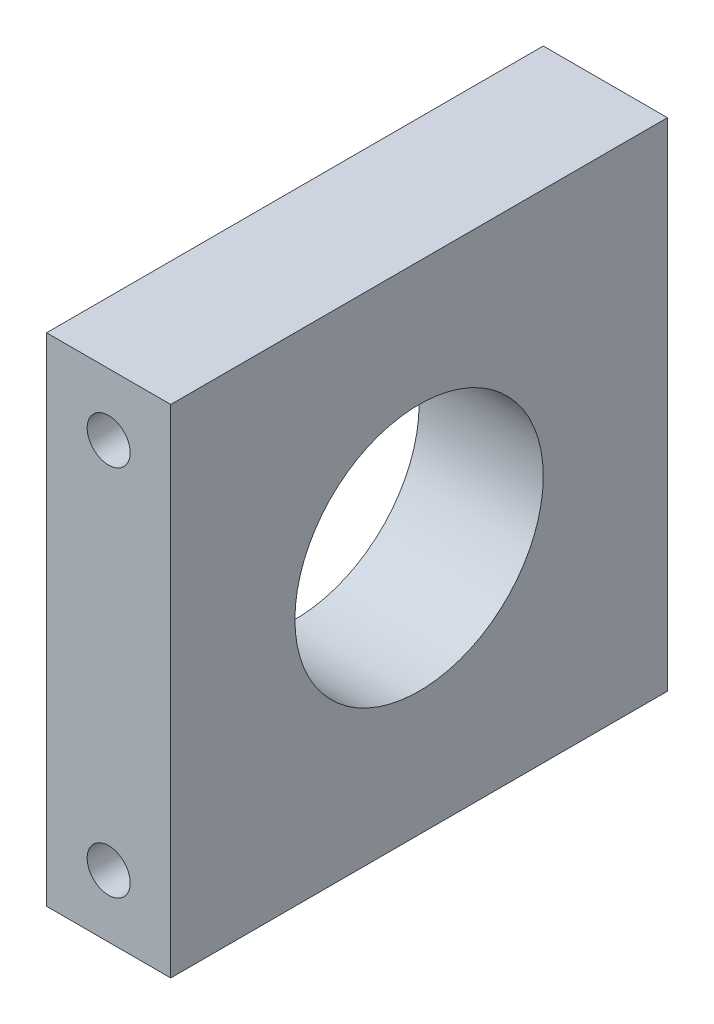
SolidWorks part; units mm, degrees
ref_plane "Front Plane" through (0, 0, 0) normal (0, 0, 1) x (1, 0, 0)
ref_plane "Top Plane" through (0, 0, 0) normal (0, 1, 0) x (1, 0, 0)
ref_plane "Right Plane" through (0, 0, 0) normal (1, 0, 0) x (0, 0, -1)
sketch "Sketch2" plane through (0, 0, 0) normal (1, 0, 0) x (0, 0, -1)
  line L1 (0, 0) -> (38.1, 0)
  line L2 (0, 0) -> (0, 38.1)
  line L3 (0, 38.1) -> (38.1, 38.1)
  line L4 (38.1, 0) -> (38.1, 38.1)
  circle A0 centre (19.05, 19.05) radius 9.525
  point P8 (0, 19.05)
  point P9 (19.05, 38.1)
  dimension "D3" = 19.05
  dimension "D1" = 38.1
  dimension "D2" = 38.1
extrude "Boss-Extrude1" add sketch "Sketch2" along normal blind 9.525
sketch "Sketch3" plane through (0, 0, -38.1) normal (0, 0, -1) x (-1, 0, 0)
  line L3 (-9.525, 38.1) -> (0, 38.1) construction
  line L4 (-9.525, 0) -> (-9.525, 38.1) construction
  point P0 (-4.7625, 33.3375)
  point P1 (-4.7625, 4.7625)
  dimension "D2" = 4.7625
  dimension "D1" = 28.575
  dimension "D3" = 4.7625
hole_wizard "M4x0.7 Tapped Hole1" positions "Sketch4" profile "Sketch5" tap size "M4x0.7" standard "ANSI Metric" end condition through all
sketch "Sketch4" plane through (0, 0, -38.1) normal (0, 0, -1) x (-1, 0, 0)
  point P0 (-4.7625, 33.3375)
  point P3 (-4.7625, 4.7625)
sketch "Sketch5" plane through (4.7625, 33.3375, -38.1) normal (1, 0, 0) x (0, 1, 0)
  line L0 (0, 0) -> (0, 38.1)
  line L1 (0, 38.1) -> (1.65, 38.1)
  line L2 (1.65, 38.1) -> (1.65, 0)
  line L5 (1.65, 0) -> (0, 0)
  line L11 (0, -6.35) -> (0, 107.95) construction
  dimension "Thru Tap Drill Dia." = 3.3
  dimension "Thru Tap Drill Depth" = 38.1
cosmetic thread "Hole Thread1" parameters "D2"=4
cosmetic thread "Hole Thread2" parameters "D2"=4
